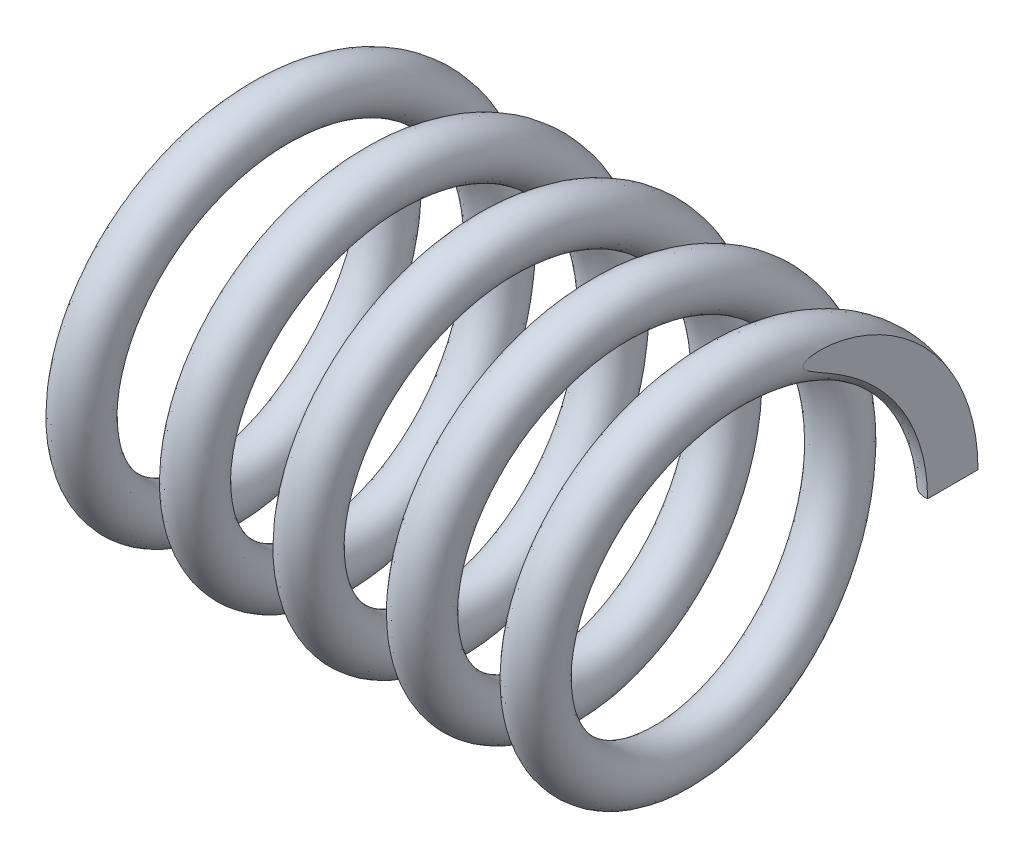
SolidWorks part; units mm, degrees
material "1.0558 (G300)"
ref_plane "Front Plane" through (0, 0, 0) normal (0, 0, 1) x (1, 0, 0)
ref_plane "Top Plane" through (0, 0, 0) normal (0, 1, 0) x (1, 0, 0)
ref_plane "Right Plane" through (0, 0, 0) normal (1, 0, 0) x (0, 0, -1)
sketch "Эскиз2" plane through (0, 0, 0) normal (1, 0, 0) x (0, 0, -1)
  circle A0 centre (0, 0) radius 28.5
  dimension "D1" = 57
curve "Спираль1" pitch 18 height 90 turns 5
sweep "По траектории1" add path "Спираль1" circular profile diameter 8 parameters "D3"=8
sketch "Эскиз3" plane through (0, 0, 0) normal (1, 0, 0) x (0, 0, -1)
  line L1 (-39.0961, 43.9471) -> (39.0961, 43.9471)
  line L2 (-39.0961, 43.9471) -> (-39.0961, -43.9471)
  line L3 (-39.0961, -43.9471) -> (39.0961, -43.9471)
  line L4 (39.0961, 43.9471) -> (39.0961, -43.9471)
  line L5 (-39.0961, 43.9471) -> (39.0961, -43.9471) construction
  line L6 (-39.0961, -43.9471) -> (39.0961, 43.9471) construction
  point P0 (0, 0)
extrude "Вырез-Вытянуть1" cut sketch "Эскиз3" against normal through all
ref_plane "Плоскость1" through (90, 0, 0) normal (1, 0, 0) x (0, 0, -1)
sketch "Эскиз4" plane through (90, 0, 0) normal (1, 0, 0) x (0, 0, -1)
  line L1 (-41.2966, -41.4302) -> (41.2966, -41.4302)
  line L2 (-41.2966, -41.4302) -> (-41.2966, 41.4302)
  line L3 (-41.2966, 41.4302) -> (41.2966, 41.4302)
  line L4 (41.2966, -41.4302) -> (41.2966, 41.4302)
  line L5 (-41.2966, -41.4302) -> (41.2966, 41.4302) construction
  line L6 (-41.2966, 41.4302) -> (41.2966, -41.4302) construction
  point P0 (0, 0)
extrude "Вырез-Вытянуть2" cut sketch "Эскиз4" along normal through all
sketch "Эскиз5" plane through (0, 0, 0) normal (0, 1, 0) x (1, 0, 0)
  line L0 (0, 0) -> (90, 0) construction
  line L2 (0, -28.5) -> (0, 28.5) construction
  line L3 (90, -39.1222) -> (90, 39.1222) construction
  point P4 (0, 0)
